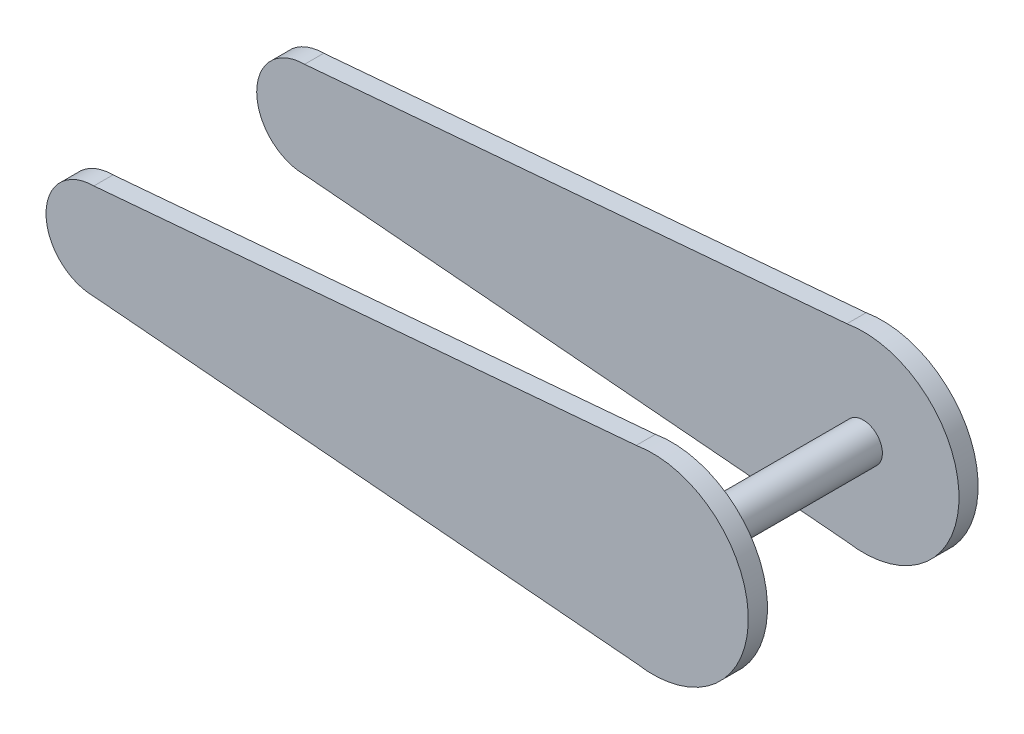
SolidWorks part; units mm, degrees
material "Aleación de cobre-cobalto-Beryllium, UNS C17500"
ref_plane "Alzado" through (0, 0, 0) normal (0, 0, 1) x (1, 0, 0)
ref_plane "Planta" through (0, 0, 0) normal (0, 1, 0) x (1, 0, 0)
ref_plane "Vista lateral" through (0, 0, 0) normal (1, 0, 0) x (0, 0, -1)
sketch "Croquis1" plane through (0, 0, 0) normal (0, 0, 1) x (1, 0, 0)
  circle A0 centre (0, 0) radius 3
extrude "Saliente-Extruir1" add sketch "Croquis1" along normal blind 18
sketch "Croquis2" plane through (0, 0, 0) normal (0, 0, 1) x (1, 0, 0)
  circle A0 centre (0, 0) radius 3
extrude "Saliente-Extruir2" add sketch "Croquis2" against normal blind 18
sketch "Croquis3" plane through (0, 0, 0) normal (1, 0, 0) x (0, 0, -1)
  line L0 (-18, 0) -> (-18, 15)
  line L1 (-18, 3) -> (-18, -3) construction
  line L2 (-18, 15) -> (-15, 15)
  line L3 (-15, 15) -> (-15, -15)
  line L4 (-15, -15) -> (-18, -15)
  line L5 (-18, -15) -> (-18, 0)
  line L6 (0, 0) -> (0, 0.7969)
  line L7 (0, -5.0594) -> (0, 7.5)
  line L8 (18, -15) -> (18, 0)
  line L9 (15, -15) -> (18, -15)
  line L10 (15, 15) -> (15, -15)
  line L11 (18, 15) -> (15, 15)
  line L12 (18, 0) -> (18, 15)
extrude "Saliente-Extruir3" add sketch "Croquis3" along normal blind 15 contours L5 L4 L3 L2 L0 | L12 L11 L10 L9 L8
sketch "Croquis4" plane through (0, 0, 0) normal (1, 0, 0) x (0, 0, -1)
  line L0 (18, 15) -> (15, 15)
  line L1 (15, 15) -> (15, -15)
  line L2 (15, -15) -> (18, -15)
  line L3 (18, -15) -> (18, 15)
  line L4 (-15, 15) -> (-18, 15)
  line L5 (-18, 15) -> (-18, -15)
  line L6 (-18, -15) -> (-15, -15)
  line L7 (-15, -15) -> (-15, 15)
extrude "Saliente-Extruir4" add sketch "Croquis4" against normal blind 95
ref_plane "Plano1" through (0, 0, 18) normal (0, 0, 1) x (1, 0, 0)
sketch "Croquis5" plane through (0, 0, 18) normal (0, 0, 1) x (1, 0, 0)
  line L1 (-95, 15) -> (-95, -15) construction
  line L2 (-87.5, 7.5) -> (0, 15)
  line L3 (0, -15) -> (-87.5, -7.5)
  line L4 (-95, 0) -> (-95, -15)
  line L5 (-95, -15) -> (0, -15)
  line L6 (0, -15) -> (15, -15)
  line L7 (15, -15) -> (15, 15)
  line L8 (15, 15) -> (-95, 15)
  line L9 (-95, 15) -> (-95, -15)
  line L10 (-95, -15) -> (-95.495, -15.0063)
  arc A0 (-87.5, 7.5) -> (-87.5, -7.5) centre (-87.5, 0) ccw
  arc A1 (-2.5527, -14.7812) -> (-2.5527, 14.7812) centre (0, 0) ccw
extrude "Cortar-Extruir1" cut sketch "Croquis5" against normal blind 95 contours A1 L8 L9 A0 L2 | A1 L3 A0 L4 L5 | A1 L6 L7 | A1 L7 L8
